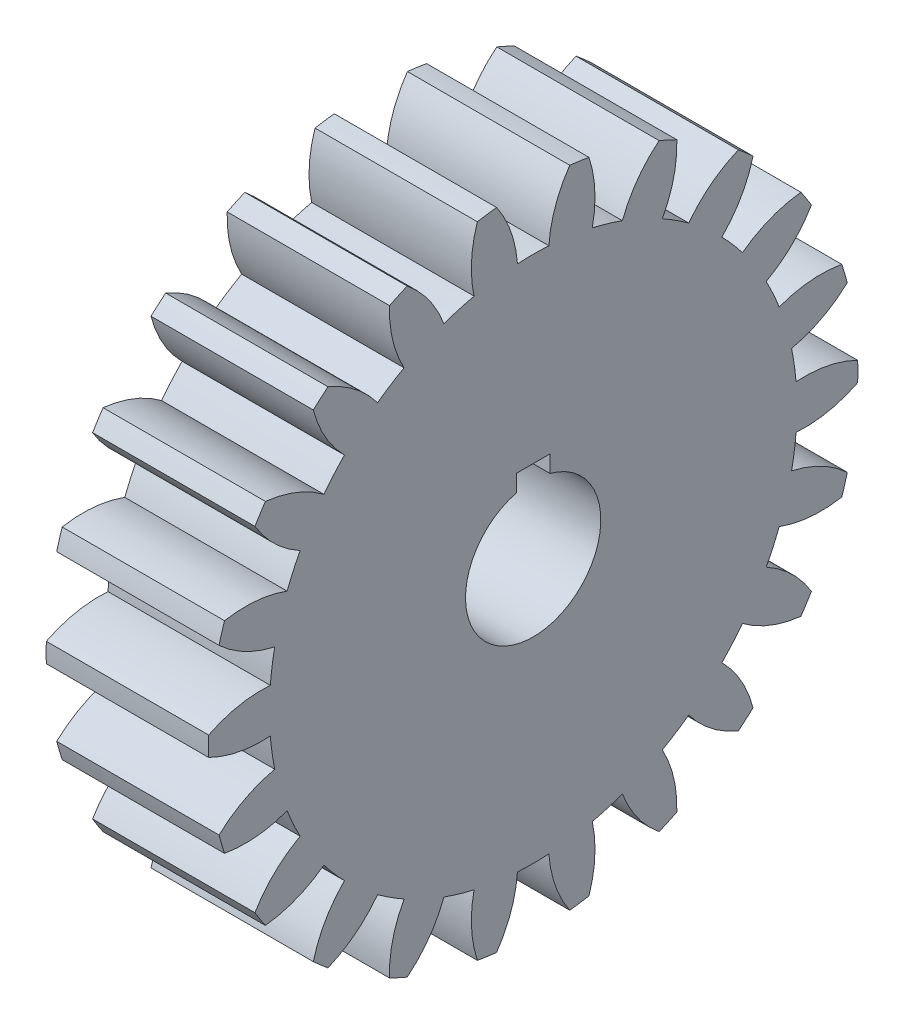
SolidWorks part; units mm, degrees
ref_plane "Plane1" through (0, 0, 0) normal (0, 0, 1) x (1, 0, 0)
ref_plane "Plane2" through (0, 0, 0) normal (0, 1, 0) x (1, 0, 0)
ref_plane "Plane3" through (0, 0, 0) normal (1, 0, 0) x (0, 0, -1)
other "Configuration Table"
sketch "HoldingSke" plane through (0, 0, 0) normal (0, 1, 0) x (1, 0, 0)
  line L0 (0, 0) -> (11.7752, -4.7575)
  line L1 (-15, 0) -> (100, 0) construction
  line L2 (0, 0) -> (-2.1039, 2.3779)
  line L3 (0, 0) -> (-11.863, 4.5341)
  line L4 (0, 0) -> (8.0072, 3.2351)
  line L5 (0, 0) -> (-47.5972, -17.7524)
  line L6 (0, 0) -> (-252.6679, -170.4757)
  line L7 (-2.1039, 2.3779) -> (63.5041, 300.0332)
  line L8 (-76.2, 54.61) -> (205.6384, 54.61)
  line L9 (-67.7845, 28.3722) -> (-49.3413, 33.142)
  line L10 (-76.2, 71.12) -> (104.1128, 71.12)
  line L11 (0, 0) -> (-304.8, 0)
  line L12 (-76.2, 101.6) -> (-74.295, 101.6)
  line L13 (24.9733, 27.94) -> (52.9518, 28.4284)
  line L14 (24.9733, 27.94) -> (24.9746, 27.94)
  line L15 (24.9733, 27.94) -> (100.4006, 29.5858)
  circle A0 centre (0, 0) radius 127
  circle A1 centre (0, 0) radius 38.1
  circle A2 centre (0, 0) radius 38.1
  circle A3 centre (0, 0) radius 127
  dimension "MHD" = 76.2
  dimension "Hub_dia" = 76.2
  dimension "Bore" = 254
  dimension "MBD" = 254
  dimension "Num_teeth" = 22
  dimension "Pitch" = 12.7
  dimension "Overall_len" = 50.8
  dimension "Show_teeth" = 22
  dimension "Thickness" = 304.8
  dimension "OAL" = 304.8001
  dimension "T_dim" = 281.8384
  dimension "Ap" = 14.5
  dimension "H" = 19.05
  dimension "Pitch_radius" = 180.3128
  dimension "Width" = 304.8
  dimension "Backlash" = 1.905
  dimension "Addendum_fac" = 1
  dimension "Dedendum_fac" = 1.25
  dimension "Clearance_fac" = 0.25
  dimension "Dedendum_add" = 0.0013
sketch "BasProSke" plane through (0, 0, 0) normal (0, 1, 0) x (1, 0, 0)
  line L0 (-10, 0) -> (60, 0) construction
  line L1 (0, 0) -> (0, 609.6)
  line L2 (0, 0) -> (304.8, 0)
  line L3 (304.8, 0) -> (304.8, 609.6)
  line L4 (304.8, 609.6) -> (0, 609.6)
  dimension "Thickness" = 304.8
  dimension "Diameter" = 1219.2
revolve "Base-Revolve" add sketch "BasProSke" angle 360 about L0
sketch "TooCutSke" plane through (0, 0, 0) normal (1, 0, 0) x (0, 0, -1)
  line L1 (0, 0) -> (0, 107) construction
  line L2 (0, 0) -> (-43.1967, 557.1279) construction
  line L3 (0, 0) -> (-158.7108, 1103.8581) construction
  line L4 (-43.1967, 557.1279) -> (-79.3554, 551.929) construction
  arc A0 (29.4779, 494.4208) -> (-29.4779, 494.4208) centre (0, 0) ccw
  arc A1 (68.6658, 605.7459) -> (-68.6658, 605.7459) centre (0, 0) ccw
  circle A2 centre (0, 0) radius 558.8 construction
  circle A3 centre (0, 0) radius 541.0009 construction
  arc A4 (-29.4779, 494.4208) -> (-68.6658, 605.7459) centre (-252.4301, 478.4987) ccw
  arc A5 (68.6658, 605.7459) -> (29.4779, 494.4208) centre (252.4301, 478.4987) ccw
  dimension "Root_dia" = 990.5975
  dimension "Overcut_dia" = 1219.2508
  dimension "Pitch_dia" = 1117.6
  dimension "Base_dia" = 1082.0018
  dimension "Flank_rad" = 223.52
  dimension "Half_ang" = 8.182
  dimension "Half_CT" = 36.5306
extrude "ToothCut" cut sketch "TooCutSke" along normal through all
fillet "Breaks" [suppressed] radius 1.016
fillet "RootFillets" [suppressed] radius 12.7013
pattern_circular "TeethCuts" count 22 every 16.364 about axis through (-10, 0, 0) along (1, 0, 0) of "ToothCut", "RootFillets", "Breaks"
sketch "HubNeaOneSke" plane through (0, 0, 0) normal (-1, 0, 0) x (0, 0, 1)
  circle A0 centre (0, 0) radius 38.1
  dimension "Diameter" = 76.2
extrude "HubNearOne" [suppressed] add sketch "HubNeaOneSke" along normal blind 25.4001
sketch "HubNeaBotSke" plane through (0, 0, 0) normal (-1, 0, 0) x (0, 0, 1)
  circle A0 centre (0, 0) radius 38.1
  dimension "Diameter" = 76.2
extrude "HubNearBoth" [suppressed] add sketch "HubNeaBotSke" along normal blind 12.7
ref_plane "FarPln" through (304.8, 0, 0) normal (1, 0, 0) x (0, 0, -1)
sketch "HubFarSke" plane through (304.8, 0, 0) normal (1, 0, 0) x (0, 0, -1)
  circle A0 centre (0, 0) radius 38.1
  dimension "Diameter" = 76.2
extrude "HubFar" [suppressed] add sketch "HubFarSke" along normal blind 12.7
sketch "BorSke" plane through (0, 0, 0) normal (1, 0, 0) x (0, 0, -1)
  circle A0 centre (0, 0) radius 127
  dimension "Diameter" = 254
extrude "Bore" cut sketch "BorSke" along normal mid plane 609.6001
sketch "KeySke" plane through (0, 0, 0) normal (1, 0, 0) x (0, 0, -1)
  line L0 (-31.75, 0) -> (-31.75, 154.8384)
  line L1 (-31.75, 154.8384) -> (31.75, 154.8384)
  line L2 (31.75, 154.8384) -> (31.75, 0)
  line L3 (0, 0) -> (0, 34) construction
  line L4 (-31.75, 0) -> (31.75, 0)
  dimension "Offset" = 154.8384
  dimension "Width" = 63.5
extrude "Keyway" cut sketch "KeySke" along normal mid plane 609.6001
pattern_circular "Keyway2" [suppressed] count 2 every 90 about axis through (-10, 0, 0) along (1, 0, 0)
equation "' \"Pitch@HoldingSke\" = 4"
equation "' \"Num_teeth@HoldingSke\" = 12"
equation "' \"Ap@HoldingSke\" =  20"
equation "' \"Ap@HoldingSke\" = 20"
equation "' \"Width@HoldingSke\" = 0.5"
equation "' \"Hub_dia@HoldingSke\"= 1"
equation "' \"Hub_dia@HoldingSke\" = 1"
equation "' \"Overall_len@HoldingSke\" = 1.0"
equation "' \"Bore@HoldingSke\" = 0.75"
equation "' \"T_dim@HoldingSke\" = 0.85"
equation "' \"Width@KeySke\" = 0.25"
equation "' \"Show_teeth@HoldingSke\" = 13"
equation "' \"Backlash@HoldingSke\" = 0.009"
equation "' \"Addendum_fac@HoldingSke\" = 1.0"
equation "' \"Dedendum_fac@HoldingSke\" = 1.25"
equation "' \"Dedendum_add@HoldingSke\" = 0.00005"
equation "' \"Clearance_fac@HoldingSke\" = 0.25"
equation "' \"Pitch@HoldingSke\" = 0.5"
equation "' \"Num_teeth@HoldingSke\" = 23"
equation "' \"Show_teeth@HoldingSke\" = 23"
equation "' \"Backlash@HoldingSke\" = 0.0375"
equation "\"Overcut_dia@TooCutSke\" = (\"Num_teeth@HoldingSke\" + 2 * \"Addendum_fac@HoldingSke\") / \"Pitch@HoldingSke\" + 0.002"
equation "\"Pitch_dia@TooCutSke\" = \"Num_teeth@HoldingSke\" / \"Pitch@HoldingSke\""
equation "\"Base_dia@TooCutSke\" = \"Num_teeth@HoldingSke\" / \"Pitch@HoldingSke\" * cos((\"Ap@HoldingSke\"  * 3.14159265 / 180))"
equation "\"Root_dia@TooCutSke\" = (\"Num_teeth@HoldingSke\" + 2) / \"Pitch@HoldingSke\" - 2 * (\"Addendum_fac@HoldingSke\" + \"Dedendum_fac@HoldingSke\") / \"Pitch@HoldingSke\" - \"Dedendum_add@HoldingSke\" * 2"
equation "\"Half_ang@TooCutSke\" = 180 / \"Num_teeth@HoldingSke\""
equation "\"Half_CT@TooCutSke\" = \"Num_teeth@HoldingSke\" / \"Pitch@HoldingSke\" * sin((3.14159265 / 2 / \"Num_teeth@HoldingSke\")) / 2 - 7 * \"Backlash@HoldingSke\" / 4"
equation "\"Flank_rad@TooCutSke\" = \"Num_teeth@HoldingSke\" / \"Pitch@HoldingSke\" / 5"
equation "\"Radius@RootFillets\" = \"Clearance_fac@HoldingSke\" / \"Pitch@HoldingSke\" + \"Dedendum_add@HoldingSke\""
equation "\"Break_rad@Breaks\" = 0.02 / \"Pitch@HoldingSke\""
equation "\"Thickness@HoldingSke\" = \"Width@HoldingSke\""
equation "\"OAL@HoldingSke\" = \"Thickness@HoldingSke\""
equation "\"MHD@HoldingSke\" = (\"Num_teeth@HoldingSke\" + 2) / \"Pitch@HoldingSke\" - 2 * (\"Addendum_fac@HoldingSke\" + \"Dedendum_fac@HoldingSke\")  / \"Pitch@HoldingSke\" - \"Dedendum_add@HoldingSke\" * 2"
equation "\"MBD@HoldingSke\" = (\"Num_teeth@HoldingSke\" + 2) / \"Pitch@HoldingSke\" - 2 * (\"Addendum_fac@HoldingSke\" + \"Dedendum_fac@HoldingSke\")  / \"Pitch@HoldingSke\" - \"Dedendum_add@HoldingSke\" * 2 - 0.002"
equation "\"MHD@HoldingSke\" = ((sgn( \"MHD@HoldingSke\" - \"Hub_dia@HoldingSke\" )-1)*( \"MHD@HoldingSke\" - \"Hub_dia@HoldingSke\" ))/-2+ \"Hub_dia@HoldingSke\""
equation "\"MBD@HoldingSke\" = ((sgn( \"MBD@HoldingSke\" - \"Bore@HoldingSke\" )-1)*( \"MBD@HoldingSke\" - \"Bore@HoldingSke\" ))/-2+ \"Bore@HoldingSke\""
equation "\"OAL@HoldingSke\" = ((sgn( \"OAL@HoldingSke\" - \"Overall_len@HoldingSke\" )+1)*( \"OAL@HoldingSke\" - \"Overall_len@HoldingSke\" ))/2 + \"Overall_len@HoldingSke\" + 0.000002"
equation "\"Num_teeth@TeethCuts\" = int( \"Show_teeth@HoldingSke\" ) + 1"
equation "\"Num_teeth@TeethCuts\" = ((sgn( \"Num_teeth@TeethCuts\" - \"Num_teeth@HoldingSke\" )-1)*( \"Num_teeth@TeethCuts\" - \"Num_teeth@HoldingSke\" ))/-2+ \"Num_teeth@HoldingSke\""
equation "\"Num_teeth@TeethCuts\" = ((sgn( \"Num_teeth@TeethCuts\" - 2.0)+1)*( \"Num_teeth@TeethCuts\" - 2.0))/2 +2.0"
equation "\"Angle@TeethCuts\" = 360.0 / \"Num_teeth@HoldingSke\""
equation "\"Diameter@BasProSke\" = (\"Num_teeth@HoldingSke\" + 2 * \"Addendum_fac@HoldingSke\") / \"Pitch@HoldingSke\""
equation "\"Thickness@BasProSke\"  = \"Thickness@HoldingSke\""
equation "' \"Fillet_rad@BasProSke\" =  \"Thickness@HoldingSke\" * 0.05"
equation "' \"Fillet_rad@BasProSke\" = \"Thickness@HoldingSke\" * 0.05"
equation "\"MHD@HoldingSke\" = ((sgn( \"MHD@HoldingSke\" - \"Root_dia@TooCutSke\" )-1)*( \"MHD@HoldingSke\" - \"Root_dia@TooCutSke\" ))/-2+ \"Root_dia@TooCutSke\""
equation "\"Diameter@HubNeaOneSke\" = \"MHD@HoldingSke\""
equation "\"Length@HubNearOne\" = \"OAL@HoldingSke\" - \"Thickness@BasProSke\""
equation "\"Diameter@HubNeaBotSke\" = \"MHD@HoldingSke\""
equation "\"Length@HubNearBoth\" = ( \"OAL@HoldingSke\" - \"Thickness@BasProSke\" ) / 2.0"
equation "\"Thickness@FarPln\" = \"Thickness@BasProSke\""
equation "\"Diameter@HubFarSke\" = \"MHD@HoldingSke\""
equation "\"Length@HubFar\" = ( \"OAL@HoldingSke\" - \"Thickness@BasProSke\" ) / 2.0"
equation "\"Diameter@BorSke\" = \"MBD@HoldingSke\""
equation "\"D1@Bore\" = \"OAL@HoldingSke\" * 2.0"
equation "\"D1@Keyway\" = \"OAL@HoldingSke\" * 2.0"
equation "\"Offset@KeySke\" = \"T_dim@HoldingSke\" - \"MBD@HoldingSke\" / 2.0"
